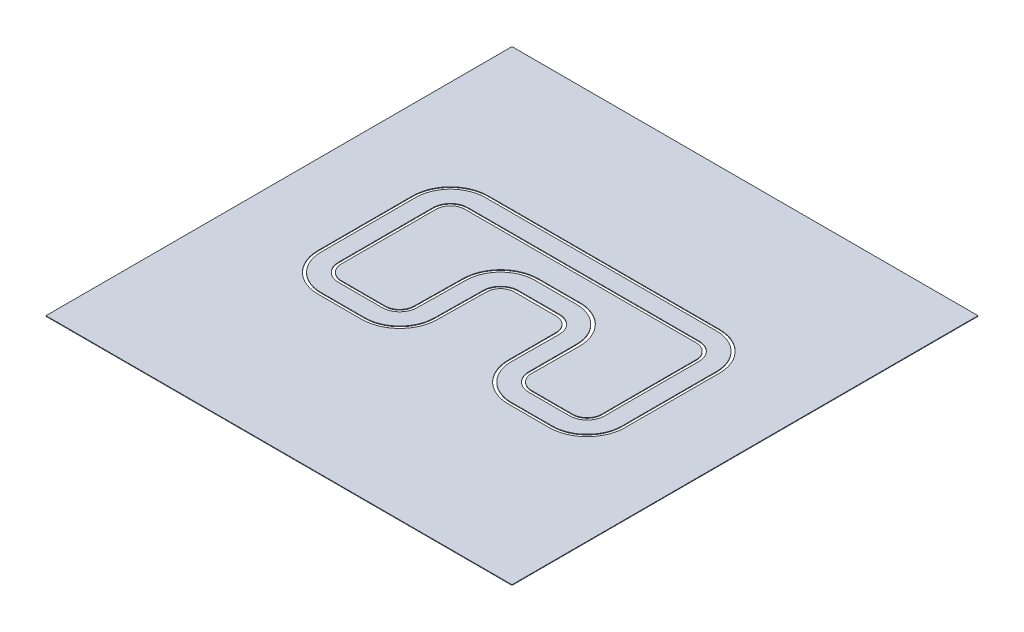
SolidWorks part; units mm, degrees
ref_plane "Front Plane" through (0, 0, 0) normal (0, 0, 1) x (1, 0, 0)
ref_plane "Top Plane" through (0, 0, 0) normal (0, 1, 0) x (1, 0, 0)
ref_plane "Right Plane" through (0, 0, 0) normal (1, 0, 0) x (0, 0, -1)
sketch "Sketch1" plane through (0, 0, 0) normal (0, 1, 0) x (1, 0, 0)
  line L1 (-4000, 4000) -> (4000, 4000)
  line L2 (-4000, 4000) -> (-4000, -4000)
  line L3 (-4000, -4000) -> (4000, -4000)
  line L4 (4000, 4000) -> (4000, -4000)
  line L6 (-2284.5119, 928.049) -> (-2284.5119, 128.049)
  line L10 (-2234.5119, 928.049) -> (-2234.5119, 128.049)
  line L14 (-2584.5119, 928.049) -> (-2584.5119, 128.049)
  line L18 (-2634.5119, 928.049) -> (-2634.5119, 128.049)
  line L32 (-332.4408, 372.8129) -> (381.5186, 372.8129)
  line L33 (-633.3097, -694.4734) -> (-622.4659, 132.4739)
  line L34 (-2234.5119, 128.049) -> (-2234.5119, -694.4734)
  line L36 (-972.5239, 127.9783) -> (-983.3097, -694.4734)
  line L37 (-933.3097, -694.4734) -> (-922.5239, 128.049)
  line L39 (-2284.5119, -694.4734) -> (-2284.5119, 128.049)
  line L40 (-2584.5119, -694.4734) -> (-2584.5119, 128.049)
  line L42 (-572.4202, 135.9598) -> (-583.3097, -694.4734)
  line L44 (-2634.5119, 128.049) -> (-2634.5119, -694.4734)
  line L46 (1032.8985, 128.049) -> (1027.7123, -689.3093)
  line L49 (977.7123, -689.3093) -> (977.7123, 133.2132)
  line L52 (677.7343, -694.4734) -> (683.4477, 128.049)
  line L55 (627.733, 128.0074) -> (627.733, -694.515)
  line L57 (-322.4917, 428.5403) -> (382.9675, 428.5403)
  line L58 (-276.5352, 722.8147) -> (382.969, 722.8147)
  line L59 (-322.4092, 776.3575) -> (338.3939, 776.3575)
  line L64 (-1984.5119, -944.4734) -> (-1233.3097, -944.4734)
  line L66 (-1984.5119, -994.4734) -> (-1233.3097, -994.4734)
  line L68 (-1984.5119, -1294.4734) -> (-1233.3097, -1294.4734)
  line L69 (-1984.5119, -1344.4734) -> (-1233.3097, -1344.4734)
  line L70 (1282.8765, -1344.4734) -> (1984.5119, -1344.4734)
  line L71 (1282.8985, -1294.4734) -> (1984.5119, -1294.4734)
  line L72 (1282.8985, -994.4734) -> (1984.5119, -994.4734)
  line L73 (1282.8985, -944.4734) -> (1984.5119, -944.4734)
  line L74 (-1984.5119, 1178.049) -> (1984.5119, 1178.049)
  line L75 (2584.5119, 928.049) -> (2584.5119, 128.049)
  line L76 (2634.5119, 928.049) -> (2634.5119, 128.049)
  line L77 (2584.5119, -694.4734) -> (2584.5119, 128.049)
  line L78 (2634.5119, 128.049) -> (2634.5119, -694.4734)
  line L79 (-1984.5119, 1228.049) -> (1984.5119, 1228.049)
  line L80 (-1984.5119, 1528.049) -> (1984.5119, 1528.049)
  line L81 (-1984.5119, 1578.049) -> (1984.5119, 1578.049)
  line L83 (-4000, 4000) -> (-4000, -4000)
  line L84 (4000, 4000) -> (4000, -4000)
  line L85 (2234.5119, 128.049) -> (2234.5119, -694.4734)
  line L86 (2284.5119, -694.4734) -> (2284.5119, 128.049)
  line L87 (2234.5119, 928.049) -> (2234.5119, 128.049)
  line L88 (2284.5119, 928.049) -> (2284.5119, 128.049)
  arc A3 (-1984.5119, 1228.049) -> (-2284.5119, 928.049) centre (-1984.5119, 928.049) ccw
  arc A7 (-1984.5119, 1178.049) -> (-2234.5119, 928.049) centre (-1984.5119, 928.049) ccw
  arc A11 (-1984.5119, 1528.049) -> (-2584.5119, 928.049) centre (-1984.5119, 928.049) ccw
  arc A14 (-1984.5119, 1578.049) -> (-2634.5119, 928.049) centre (-1984.5119, 928.049) ccw
  arc A18 (-276.5352, 722.8147) -> (-922.5239, 128.049) centre (-322.5339, 124.5805) ccw
  arc A19 (-322.4092, 776.3575) -> (-972.5239, 127.9783) centre (-322.5259, 126.3575) ccw
  arc A24 (-1984.5119, -994.4734) -> (-2284.5119, -694.4734) centre (-1984.5119, -694.4734) cw
  arc A25 (-1984.5119, -944.4734) -> (-2234.5119, -694.4734) centre (-1984.5119, -694.4734) cw
  arc A26 (-1233.3097, -944.4734) -> (-983.3097, -694.4734) centre (-1233.3097, -694.4734) ccw
  arc A27 (-1233.3097, -994.4734) -> (-933.3097, -694.4734) centre (-1233.3097, -694.4734) ccw
  arc A28 (-1984.5119, -1294.4734) -> (-2584.5119, -694.4734) centre (-1984.5119, -694.4734) cw
  arc A29 (-1233.3097, -1294.4734) -> (-633.3097, -694.4734) centre (-1233.3097, -694.4734) ccw
  arc A30 (-1233.3097, -1344.4734) -> (-583.3097, -694.4734) centre (-1233.3097, -694.4734) ccw
  arc A31 (-1984.5119, -1344.4734) -> (-2634.5119, -694.4734) centre (-1984.5119, -694.4734) cw
  arc A32 (338.3939, 776.3575) -> (1032.8985, 128.049) centre (384.4179, 129.5105) cw
  arc A33 (1282.8985, -944.4734) -> (1027.7123, -689.3093) centre (1282.8765, -689.3093) cw
  arc A36 (1282.8985, -994.4734) -> (977.7123, -689.3093) centre (1282.8765, -689.3093) cw
  arc A37 (382.969, 722.8147) -> (977.7123, 133.2132) centre (384.4179, 129.5105) cw
  arc A38 (382.9675, 428.5403) -> (683.4477, 128.049) centre (384.4179, 129.5105) cw
  arc A39 (1282.8985, -1294.4734) -> (677.7343, -694.4734) centre (1282.8765, -689.3093) cw
  arc A42 (1282.8765, -1344.4734) -> (627.733, -694.515) centre (1282.8765, -689.3093) cw
  arc A43 (381.5186, 372.8129) -> (627.733, 128.0074) centre (384.4179, 129.5105) cw
  arc A44 (1984.5119, 1528.049) -> (2584.5119, 928.049) centre (1984.5119, 928.049) cw
  arc A45 (1984.5119, 1578.049) -> (2634.5119, 928.049) centre (1984.5119, 928.049) cw
  arc A46 (1984.5119, -1294.4734) -> (2584.5119, -694.4734) centre (1984.5119, -694.4734) ccw
  arc A47 (1984.5119, -1344.4734) -> (2634.5119, -694.4734) centre (1984.5119, -694.4734) ccw
  arc A48 (1984.5119, -944.4734) -> (2234.5119, -694.4734) centre (1984.5119, -694.4734) ccw
  arc A49 (1984.5119, -994.4734) -> (2284.5119, -694.4734) centre (1984.5119, -694.4734) ccw
  arc A50 (1984.5119, 1228.049) -> (2284.5119, 928.049) centre (1984.5119, 928.049) cw
  arc A51 (1984.5119, 1178.049) -> (2234.5119, 928.049) centre (1984.5119, 928.049) cw
  arc A52 (-332.4408, 372.8129) -> (-572.4202, 135.9598) centre (-332.4408, 132.8129) ccw
  arc A53 (-322.4917, 428.5403) -> (-622.4659, 132.4739) centre (-322.4917, 128.5403) ccw
  point P4 (0, 4000)
  point P6 (-4000, 0)
  dimension "D3" = 822.5224
  dimension "D4" = 243.3197
  dimension "D6" = 240
  dimension "D7" = 300
  dimension "D1" = 8000
  dimension "D2" = 8000
  dimension "D5" = 50
  dimension "D9" = 300
  dimension "D18" = 50
extrude "Boss-Extrude1" add sketch "Sketch1" along normal blind 10 contours L4 L1 L2 L3 L32 A52 L42 A30 L69 A31 L44 L18 A14 L81 A45 L76 L78 A47 L70 A42 L55 A43 | A53 L57 A38 L52 A39 L71 A46 L77 L75 A44 L80 A11 L14 L40 A28 L68 A29 L33 L79 A50 L88 L86 A49 L72 A36 L49 A37 L58 A18 L37 A27 L66 A24 L39 L6 A3 | A51 L74 A7 L10 L34 A25 L64 A26 L36 A19 L59 A32 L46 A33 L73 A48 L85 L87
